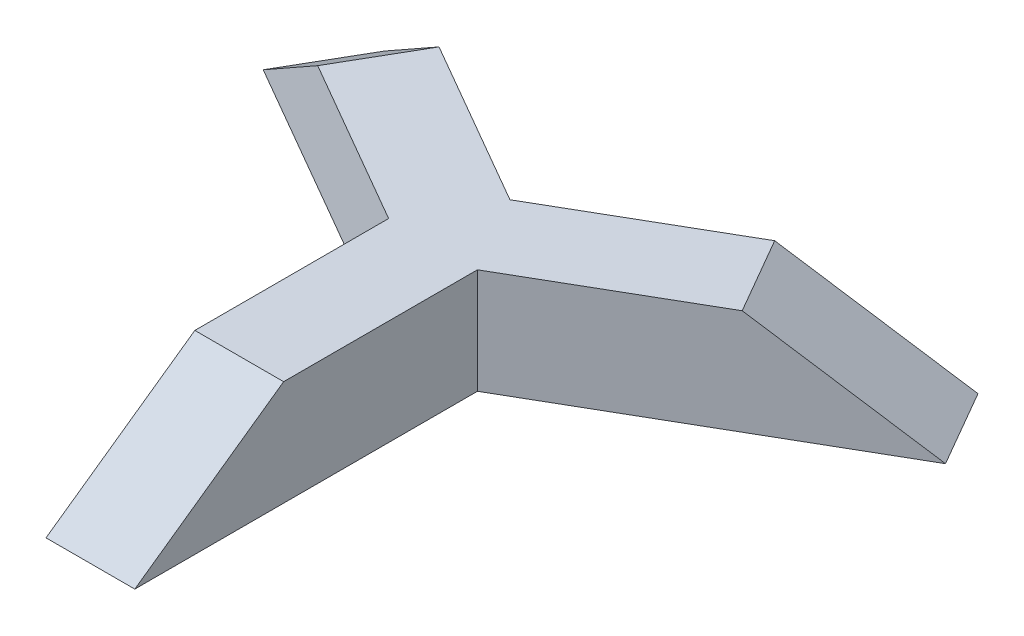
SolidWorks part; units mm, degrees
ref_plane "Front Plane" through (0, 0, 0) normal (0, 0, 1) x (1, 0, 0)
ref_plane "Top Plane" through (0, 0, 0) normal (0, 1, 0) x (1, 0, 0)
ref_plane "Right Plane" through (0, 0, 0) normal (1, 0, 0) x (0, 0, -1)
sketch "Sketch3" plane through (0, 0, 0) normal (0, 1, 0) x (1, 0, 0)
  line L0 (-21.1, -12.1821) -> (-21.1, -175)
  line L1 (21.1, -12.1821) -> (0, 24.3642) construction
  line L2 (0, 24.3642) -> (-21.1, -12.1821) construction
  line L3 (-21.1, -12.1821) -> (21.1, -12.1821) construction
  line L4 (-21.1, -175) -> (21.1, -175)
  line L5 (21.1, -175) -> (21.1, -12.1821)
  line L6 (-21.1, -12.1821) -> (0, 0)
  line L7 (0, 0) -> (21.1, -12.1821)
  circle A0 centre (0, 0) radius 12.1821 construction
  dimension "D1" = 42.2
  dimension "D2" = 175
extrude "Boss-Extrude2" add sketch "Sketch3" along normal blind 50
sketch "Sketch4" plane through (-21.1, 0, 0) normal (-1, 0, 0) x (0, 0, 1)
  line L0 (175, 0) -> (104.2778, 50)
  line L1 (12.1821, 50) -> (175, 50) construction
  line L2 (104.2778, 50) -> (175, 50)
  line L3 (175, 50) -> (175, 0)
  dimension "D1" = 54.74
extrude "Cut-Extrude1" cut sketch "Sketch4" against normal up to next (42.2 mm away)
pattern_circular "CirPattern1" count 3 every 120 about axis through (0, 0, 0) along (0, 1, 0) of "Boss-Extrude2", "Cut-Extrude1"
